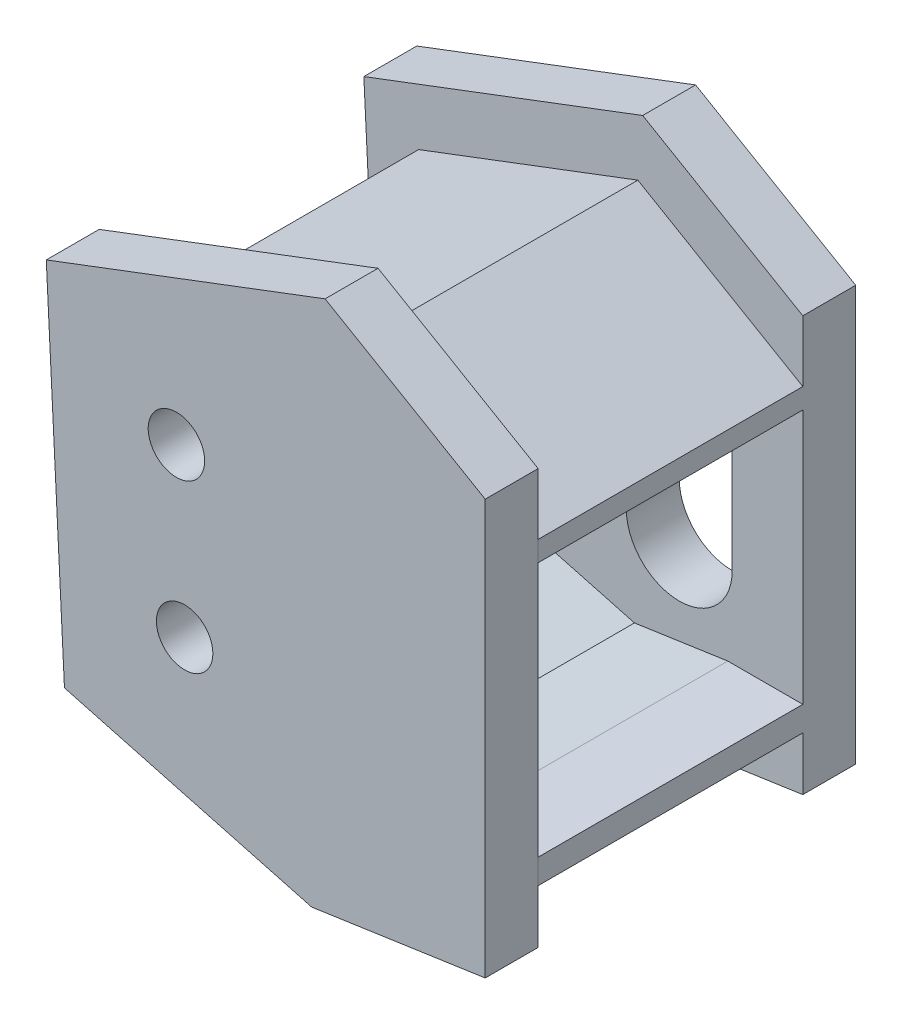
SolidWorks part; units mm, degrees
material "PET"
ref_plane "前视基准面" through (0, 0, 0) normal (0, 0, 1) x (1, 0, 0)
ref_plane "上视基准面" through (0, 0, 0) normal (0, 1, 0) x (1, 0, 0)
ref_plane "右视基准面" through (0, 0, 0) normal (1, 0, 0) x (0, 0, -1)
sketch "草图1" plane through (0, 0, 0) normal (0, 0, 1) x (1, 0, 0)
  line L0 (0, 4) -> (0, 0) construction
  line L1 (-9.6593, 2.5882) -> (0, 0) construction
  line L2 (-9.3506, 26.4551) -> (0, 30) construction
  line L3 (0, 21) -> (0, 19.8513)
  line L4 (-9.6593, 2.5882) -> (-20.9623, 5.6168)
  line L5 (-21.7739, 21.7454) -> (-9.3506, 26.4551)
  line L6 (0, 4) -> (-9.6593, 2.5882)
  line L7 (-9.3506, 26.4551) -> (0, 21)
  line L8 (-21.7739, 21.7454) -> (-20.9623, 5.6168)
  line L9 (0, 10.1744) -> (0, 30) construction
  line L10 (-33.3529, 13.078) -> (-21.3681, 13.6811) construction
  line L14 (-34.7708, 16.8182) -> (-21.7739, 21.7454) construction
  line L15 (-20.9623, 5.6168) -> (-34.3882, 9.2143) construction
  line L16 (-9.5402, 4.6268) -> (-4.2504, 5.4)
  line L17 (-2, 5.7289) -> (-4.2504, 5.4) construction
  line L18 (0, 10.1744) -> (0, 21) construction
  line L20 (-9.5341, 24.2467) -> (-2, 19.8513)
  line L21 (-2, 19.8513) -> (-2, 5.7289) construction
  line L23 (-9.5402, 4.6268) -> (-19.038, 7.1718)
  line L24 (-19.7033, 20.3915) -> (-19.038, 7.1718)
  line L25 (-19.7033, 20.3915) -> (-9.5341, 24.2467)
  line L26 (-2, 19.8513) -> (0, 19.8513)
  line L28 (0, 19.8513) -> (0, 5.4) construction
  line L29 (0, 5.4) -> (0, 4)
  line L30 (0, 21) -> (0, 4) construction
  line L31 (0, 5.4) -> (-4.2504, 5.4)
  line L33 (-2, 5.7289) -> (-9.5402, 4.6268) construction
  dimension "D1" = 12
  dimension "D2" = 9
  dimension "D3" = 10
  dimension "D4" = 4
  dimension "D5" = 10
  dimension "D7" = 1.4
  dimension "D8" = 30
  dimension "D9" = 37.1856
  dimension "D10" = 35.6013
  dimension "D11" = 249.238
  dimension "D12" = 10.8754
  dimension "D13" = 1.1487
  dimension "D14" = 14.4513
  dimension "D15" = 3.7402
  dimension "D6" = 2
extrude "凸台-拉伸1" add sketch "草图1" against normal blind 15
sketch "草图2" plane through (0, 0, -15) normal (0, 0, -1) x (-1, 0, 0)
  line L15 (0, 24.4732) -> (0, 0.9681)
  line L16 (0, 19.8513) -> (0, 21) construction
  line L20 (9.8378, -0.4698) -> (-0.4339, 1.0315)
  line L21 (23.8487, 3.2844) -> (9.8378, -0.4698)
  line L22 (24.8799, 23.7763) -> (23.8487, 3.2844)
  line L23 (9.0754, 29.7678) -> (24.8799, 23.7763)
  line L24 (-1.5117, 23.5913) -> (9.0754, 29.7678)
  line L25 (9.8378, -0.4698) -> (0, 0.9681)
  line L26 (23.8487, 3.2844) -> (9.8378, -0.4698)
  line L27 (24.8799, 23.7763) -> (23.8487, 3.2844)
  line L28 (9.0754, 29.7678) -> (24.8799, 23.7763)
  line L29 (0, 24.4732) -> (9.0754, 29.7678)
  dimension "D1" = 3
extrude "凸台-拉伸2" add sketch "草图2" along normal blind 3
sketch "草图4" plane through (0, 0, -15) normal (0, 0, 1) x (1, 0, 0)
  circle A2 centre (-17.5033, 18.3915) radius 4
  circle A3 centre (-17.038, 9.1718) radius 4
  dimension "D5" = 8
  dimension "D6" = 8
  dimension "D1" = 2.2
  dimension "D2" = 2
  dimension "D3" = 2
  dimension "D4" = 2
extrude "凸台-拉伸3" add sketch "草图4" along normal blind 15
sketch "草图5" plane through (0, 0, 0) normal (0, 0, 1) x (1, 0, 0)
  line L6 (0, 24.4732) -> (-9.0754, 29.7678)
  line L7 (0, 0.9681) -> (0, 24.4732)
  line L8 (-9.8378, -0.4698) -> (0, 0.9681)
  line L9 (-23.8487, 3.2844) -> (-9.8378, -0.4698)
  line L10 (-24.8799, 23.7763) -> (-23.8487, 3.2844)
  line L11 (-9.0754, 29.7678) -> (-24.8799, 23.7763)
  line L12 (0, 24.4732) -> (-9.0754, 29.7678)
  line L13 (0, 0.9681) -> (0, 24.4732)
  line L14 (-9.8378, -0.4698) -> (0, 0.9681)
  line L15 (-23.8487, 3.2844) -> (-9.8378, -0.4698)
  line L16 (-24.8799, 23.7763) -> (-23.8487, 3.2844)
  line L17 (-9.0754, 29.7678) -> (-24.8799, 23.7763)
  dimension "D1" = 0
extrude "凸台-拉伸4" add sketch "草图5" along normal blind 3 separate body
sketch "草图6" plane through (0, 0, 3) normal (0, 0, 1) x (1, 0, 0)
  circle A0 centre (-17.5033, 18.3915) radius 1.6
  circle A1 centre (-17.038, 9.1718) radius 1.6
  dimension "D1" = 3.2
  dimension "D2" = 3.2
extrude "切除-拉伸1" cut sketch "草图6" against normal blind 3
sketch "草图8" plane through (0, 0, -18) normal (0, 0, -1) x (-1, 0, 0)
  line L0 (7, 15.9681) -> (7, 9.9681) construction
  line L1 (10, 15.9681) -> (10, 9.9681)
  line L2 (4, 15.9681) -> (4, 9.9681)
  line L3 (0, 24.4732) -> (0, 0.9681) construction
  arc A0 (10, 15.9681) -> (4, 15.9681) centre (7, 15.9681) ccw
  arc A1 (4, 9.9681) -> (10, 9.9681) centre (7, 9.9681) ccw
  point P2 (7, 12.9681)
  dimension "D2" = 3
  dimension "D1" = 6
  dimension "D3" = 7
  dimension "D4" = 9
extrude "切除-拉伸3" cut sketch "草图8" against normal blind 3
sketch "草图9" plane through (0, 0, 0) normal (0, 0, 1) x (1, 0, 0)
  circle A0 centre (-17.5033, 18.3915) radius 2.15
  circle A1 centre (-17.038, 9.1718) radius 2.15
  dimension "D1" = 4.3
  dimension "D2" = 4.3
extrude "切除-拉伸4" cut sketch "草图9" against normal blind 1
sketch "草图10" plane through (0, 0, -1) normal (0, 0, 1) x (1, 0, 0)
  circle A0 centre (-17.5033, 18.3915) radius 1.8
  circle A1 centre (-17.038, 9.1718) radius 1.8
  dimension "D1" = 3.6
  dimension "D2" = 3.6
extrude "切除-拉伸5" cut sketch "草图10" against normal blind 10
